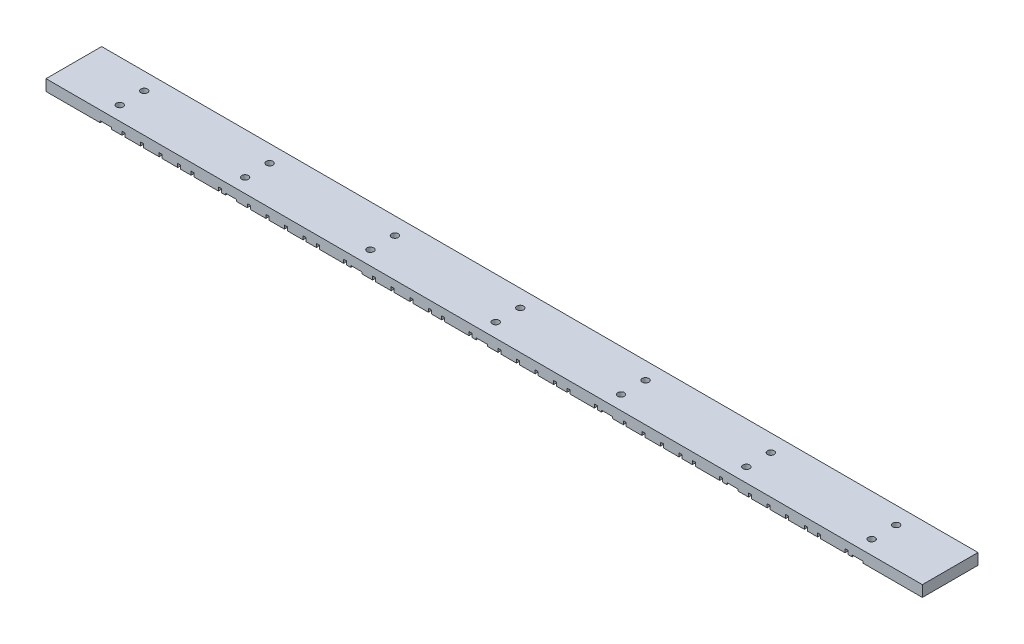
SolidWorks part; units mm, degrees
ref_plane "Front Plane" through (0, 0, 0) normal (0, 0, 1) x (1, 0, 0)
ref_plane "Top Plane" through (0, 0, 0) normal (0, 1, 0) x (1, 0, 0)
ref_plane "Right Plane" through (0, 0, 0) normal (1, 0, 0) x (0, 0, -1)
ref_plane "Plane1" through (0, 98, 0) normal (0, 1, 0) x (1, 0, 0)
sketch "Sketch2" plane through (0, 98, 0) normal (0, 1, 0) x (1, 0, 0)
  line L1 (-100, 51.75) -> (400, 51.75)
  line L2 (-100, 51.75) -> (-100, 20)
  line L3 (-100, 20) -> (400, 20)
  line L4 (400, 51.75) -> (400, 20)
extrude "Boss-Extrude1" add sketch "Sketch2" along normal blind 6.35
sketch "Sketch5" plane through (0, 0, -51.75) normal (0, 0, -1) x (-1, 0, 0)
  line L0 (-357.5571, 98) -> (-357.5571, 100.0571)
  line L1 (-357.5571, 100.0571) -> (-355.8553, 100.0571)
  line L2 (-355.8553, 100.0571) -> (-355.8553, 98)
  line L3 (-355.8553, 98) -> (-341.9571, 98)
  line L4 (-341.9571, 98) -> (-341.9571, 100.0571)
  line L5 (-341.9571, 100.0571) -> (-340.2553, 100.0571)
  line L6 (-340.2553, 100.0571) -> (-340.2553, 98)
  line L7 (-340.2553, 98) -> (-334.3571, 98)
  line L8 (-334.3571, 98) -> (-334.3571, 100.0571)
  line L9 (-334.3571, 100.0571) -> (-332.6553, 100.0571)
  line L10 (-332.6553, 100.0571) -> (-332.6553, 98)
  line L11 (-332.6553, 98) -> (-323.7571, 98)
  line L12 (-323.7571, 98) -> (-323.7571, 100.0571)
  line L13 (-323.7571, 100.0571) -> (-322.0554, 100.0571)
  line L14 (-322.0554, 100.0571) -> (-322.0554, 98)
  line L15 (-322.0554, 98) -> (-313.1572, 98)
  line L16 (-313.1572, 98) -> (-313.1572, 100.0571)
  line L17 (-313.1572, 100.0571) -> (-311.4554, 100.0571)
  line L18 (-311.4554, 100.0571) -> (-311.4554, 98)
  line L19 (-311.4554, 98) -> (-302.5571, 98)
  line L20 (-302.5571, 98) -> (-302.5571, 100.0571)
  line L21 (-302.5571, 100.0571) -> (-300.8554, 100.0571)
  line L22 (-300.8554, 100.0571) -> (-300.8554, 98)
  line L23 (-300.8554, 98) -> (-295.7895, 98)
  line L24 (-400, 98) -> (100, 98) construction
  line L25 (-295.7895, 98) -> (-295.7895, 96.6332)
  line L27 (-295.7895, 96.6332) -> (-359.0747, 96.6332)
  line L28 (-359.0747, 96.6332) -> (-359.0747, 98)
  line L29 (-359.0747, 98) -> (-357.5571, 98)
  line L30 (-286.0571, 98) -> (-286.0571, 100.0571)
  line L31 (-286.0571, 100.0571) -> (-284.3553, 100.0571)
  line L32 (-284.3553, 100.0571) -> (-284.3553, 98)
  line L33 (-284.3553, 98) -> (-270.4571, 98)
  line L34 (-270.4571, 98) -> (-270.4571, 100.0571)
  line L35 (-270.4571, 100.0571) -> (-268.7553, 100.0571)
  line L36 (-268.7553, 100.0571) -> (-268.7553, 98)
  line L37 (-268.7553, 98) -> (-262.8571, 98)
  line L38 (-262.8571, 98) -> (-262.8571, 100.0571)
  line L39 (-262.8571, 100.0571) -> (-261.1553, 100.0571)
  line L40 (-261.1553, 100.0571) -> (-261.1553, 98)
  line L41 (-261.1553, 98) -> (-252.2571, 98)
  line L42 (-252.2571, 98) -> (-252.2571, 100.0571)
  line L43 (-252.2571, 100.0571) -> (-250.5554, 100.0571)
  line L44 (-250.5554, 100.0571) -> (-250.5554, 98)
  line L45 (-250.5554, 98) -> (-241.6572, 98)
  line L46 (-241.6572, 98) -> (-241.6572, 100.0571)
  line L47 (-241.6572, 100.0571) -> (-239.9554, 100.0571)
  line L48 (-239.9554, 100.0571) -> (-239.9554, 98)
  line L49 (-239.9554, 98) -> (-231.0571, 98)
  line L50 (-231.0571, 98) -> (-231.0571, 100.0571)
  line L51 (-231.0571, 100.0571) -> (-229.3554, 100.0571)
  line L52 (-229.3554, 100.0571) -> (-229.3554, 98)
  line L53 (-229.3554, 98) -> (-224.2895, 98)
  line L54 (-224.2895, 98) -> (-224.2895, 96.6332)
  line L55 (-224.2895, 96.6332) -> (-287.5747, 96.6332)
  line L56 (-287.5747, 96.6332) -> (-287.5747, 98)
  line L57 (-287.5747, 98) -> (-286.0571, 98)
  line L58 (-214.5572, 98) -> (-214.5572, 100.0571)
  line L59 (-214.5572, 100.0571) -> (-212.8554, 100.0571)
  line L60 (-212.8554, 100.0571) -> (-212.8554, 98)
  line L61 (-212.8554, 98) -> (-198.9571, 98)
  line L62 (-198.9571, 98) -> (-198.9571, 100.0571)
  line L63 (-198.9571, 100.0571) -> (-197.2553, 100.0571)
  line L64 (-197.2553, 100.0571) -> (-197.2553, 98)
  line L65 (-197.2553, 98) -> (-191.3571, 98)
  line L66 (-191.3571, 98) -> (-191.3571, 100.0571)
  line L67 (-191.3571, 100.0571) -> (-189.6554, 100.0571)
  line L68 (-189.6554, 100.0571) -> (-189.6554, 98)
  line L69 (-189.6554, 98) -> (-180.7571, 98)
  line L70 (-180.7571, 98) -> (-180.7571, 100.0571)
  line L71 (-180.7571, 100.0571) -> (-179.0554, 100.0571)
  line L72 (-179.0554, 100.0571) -> (-179.0554, 98)
  line L73 (-179.0554, 98) -> (-170.1572, 98)
  line L74 (-170.1572, 98) -> (-170.1572, 100.0571)
  line L75 (-170.1572, 100.0571) -> (-168.4554, 100.0571)
  line L76 (-168.4554, 100.0571) -> (-168.4554, 98)
  line L77 (-168.4554, 98) -> (-159.5572, 98)
  line L78 (-159.5572, 98) -> (-159.5572, 100.0571)
  line L79 (-159.5572, 100.0571) -> (-157.8554, 100.0571)
  line L80 (-157.8554, 100.0571) -> (-157.8554, 98)
  line L81 (-157.8554, 98) -> (-152.7895, 98)
  line L82 (-152.7895, 98) -> (-152.7895, 96.6332)
  line L83 (-152.7895, 96.6332) -> (-216.0747, 96.6332)
  line L84 (-216.0747, 96.6332) -> (-216.0747, 98)
  line L85 (-216.0747, 98) -> (-214.5572, 98)
  line L86 (-143.0572, 98) -> (-143.0572, 100.0571)
  line L87 (-143.0572, 100.0571) -> (-141.3554, 100.0571)
  line L88 (-141.3554, 100.0571) -> (-141.3554, 98)
  line L89 (-141.3554, 98) -> (-127.4571, 98)
  line L90 (-127.4571, 98) -> (-127.4571, 100.0571)
  line L91 (-127.4571, 100.0571) -> (-125.7553, 100.0571)
  line L92 (-125.7553, 100.0571) -> (-125.7553, 98)
  line L93 (-125.7553, 98) -> (-119.8572, 98)
  line L94 (-119.8572, 98) -> (-119.8572, 100.0571)
  line L95 (-119.8572, 100.0571) -> (-118.1554, 100.0571)
  line L96 (-118.1554, 100.0571) -> (-118.1554, 98)
  line L97 (-118.1554, 98) -> (-109.2572, 98)
  line L98 (-109.2572, 98) -> (-109.2572, 100.0571)
  line L99 (-109.2572, 100.0571) -> (-107.5554, 100.0571)
  line L100 (-107.5554, 100.0571) -> (-107.5554, 98)
  line L101 (-107.5554, 98) -> (-98.6572, 98)
  line L102 (-98.6572, 98) -> (-98.6572, 100.0571)
  line L103 (-98.6572, 100.0571) -> (-96.9554, 100.0571)
  line L104 (-96.9554, 100.0571) -> (-96.9554, 98)
  line L105 (-96.9554, 98) -> (-88.0572, 98)
  line L106 (-88.0572, 98) -> (-88.0572, 100.0571)
  line L107 (-88.0572, 100.0571) -> (-86.3554, 100.0571)
  line L108 (-86.3554, 100.0571) -> (-86.3554, 98)
  line L109 (-86.3554, 98) -> (-81.2895, 98)
  line L110 (-81.2895, 98) -> (-81.2895, 96.6332)
  line L111 (-81.2895, 96.6332) -> (-144.5747, 96.6332)
  line L112 (-144.5747, 96.6332) -> (-144.5747, 98)
  line L113 (-144.5747, 98) -> (-143.0572, 98)
  line L114 (-71.5572, 98) -> (-71.5572, 100.0571)
  line L115 (-71.5572, 100.0571) -> (-69.8554, 100.0571)
  line L116 (-69.8554, 100.0571) -> (-69.8554, 98)
  line L117 (-69.8554, 98) -> (-55.9571, 98)
  line L118 (-55.9571, 98) -> (-55.9571, 100.0571)
  line L119 (-55.9571, 100.0571) -> (-54.2553, 100.0571)
  line L120 (-54.2553, 100.0571) -> (-54.2553, 98)
  line L121 (-54.2553, 98) -> (-48.3572, 98)
  line L122 (-48.3572, 98) -> (-48.3572, 100.0571)
  line L123 (-48.3572, 100.0571) -> (-46.6554, 100.0571)
  line L124 (-46.6554, 100.0571) -> (-46.6554, 98)
  line L125 (-46.6554, 98) -> (-37.7572, 98)
  line L126 (-37.7572, 98) -> (-37.7572, 100.0571)
  line L127 (-37.7572, 100.0571) -> (-36.0554, 100.0571)
  line L128 (-36.0554, 100.0571) -> (-36.0554, 98)
  line L129 (-36.0554, 98) -> (-27.1572, 98)
  line L130 (-27.1572, 98) -> (-27.1572, 100.0571)
  line L131 (-27.1572, 100.0571) -> (-25.4554, 100.0571)
  line L132 (-25.4554, 100.0571) -> (-25.4554, 98)
  line L133 (-25.4554, 98) -> (-16.5572, 98)
  line L134 (-16.5572, 98) -> (-16.5572, 100.0571)
  line L135 (-16.5572, 100.0571) -> (-14.8554, 100.0571)
  line L136 (-14.8554, 100.0571) -> (-14.8554, 98)
  line L137 (-14.8554, 98) -> (-9.7895, 98)
  line L138 (-9.7895, 98) -> (-9.7895, 96.6332)
  line L139 (-9.7895, 96.6332) -> (-73.0747, 96.6332)
  line L140 (-73.0747, 96.6332) -> (-73.0747, 98)
  line L141 (-73.0747, 98) -> (-71.5572, 98)
  line L142 (-0.0572, 98) -> (-0.0572, 100.0571)
  line L143 (-0.0572, 100.0571) -> (1.6446, 100.0571)
  line L144 (1.6446, 100.0571) -> (1.6446, 98)
  line L145 (1.6446, 98) -> (15.5429, 98)
  line L146 (15.5429, 98) -> (15.5429, 100.0571)
  line L147 (15.5429, 100.0571) -> (17.2447, 100.0571)
  line L148 (17.2447, 100.0571) -> (17.2447, 98)
  line L149 (17.2447, 98) -> (23.1428, 98)
  line L150 (23.1428, 98) -> (23.1428, 100.0571)
  line L151 (23.1428, 100.0571) -> (24.8446, 100.0571)
  line L152 (24.8446, 100.0571) -> (24.8446, 98)
  line L153 (24.8446, 98) -> (33.7428, 98)
  line L154 (33.7428, 98) -> (33.7428, 100.0571)
  line L155 (33.7428, 100.0571) -> (35.4446, 100.0571)
  line L156 (35.4446, 100.0571) -> (35.4446, 98)
  line L157 (35.4446, 98) -> (44.3428, 98)
  line L158 (44.3428, 98) -> (44.3428, 100.0571)
  line L159 (44.3428, 100.0571) -> (46.0446, 100.0571)
  line L160 (46.0446, 100.0571) -> (46.0446, 98)
  line L161 (46.0446, 98) -> (54.9428, 98)
  line L162 (54.9428, 98) -> (54.9428, 100.0571)
  line L163 (54.9428, 100.0571) -> (56.6446, 100.0571)
  line L164 (56.6446, 100.0571) -> (56.6446, 98)
  line L165 (56.6446, 98) -> (61.7105, 98)
  line L166 (61.7105, 98) -> (61.7105, 96.6332)
  line L167 (61.7105, 96.6332) -> (-1.5747, 96.6332)
  line L168 (-1.5747, 96.6332) -> (-1.5747, 98)
  line L169 (-1.5747, 98) -> (-0.0572, 98)
  dimension "D1" = 6
extrude "Cut-Extrude2" cut sketch "Sketch5" against normal through all
sketch "Sketch7" plane through (0, 0, -20) normal (0, 0, 1) x (1, 0, 0)
  line L0 (-70.2467, 98) -> (-69.0919, 98)
  line L1 (-100, 98) -> (-56.6446, 98) construction
  line L2 (-69.0919, 98) -> (-69.0919, 99)
  line L3 (-69.0919, 99) -> (-62.7419, 99)
  line L4 (-62.7419, 99) -> (-62.7419, 98)
  line L5 (-62.7419, 98) -> (-61.7747, 98)
  line L6 (-61.7747, 98) -> (-61.7747, 96.8336)
  line L7 (-61.7747, 96.8336) -> (-70.2467, 96.8336)
  line L8 (-70.2467, 96.8336) -> (-70.2467, 98)
  line L9 (1.2533, 98) -> (2.4081, 98)
  line L10 (2.4081, 98) -> (2.4081, 99)
  line L11 (2.4081, 99) -> (8.7581, 99)
  line L12 (8.7581, 99) -> (8.7581, 98)
  line L13 (8.7581, 98) -> (9.7253, 98)
  line L14 (9.7253, 98) -> (9.7253, 96.8336)
  line L15 (9.7253, 96.8336) -> (1.2533, 96.8336)
  line L16 (1.2533, 96.8336) -> (1.2533, 98)
  line L17 (72.7533, 98) -> (73.9081, 98)
  line L18 (73.9081, 98) -> (73.9081, 99)
  line L19 (73.9081, 99) -> (80.2581, 99)
  line L20 (80.2581, 99) -> (80.2581, 98)
  line L21 (80.2581, 98) -> (81.2253, 98)
  line L22 (81.2253, 98) -> (81.2253, 96.8336)
  line L23 (81.2253, 96.8336) -> (72.7533, 96.8336)
  line L24 (72.7533, 96.8336) -> (72.7533, 98)
  line L25 (144.2533, 98) -> (145.4081, 98)
  line L26 (145.4081, 98) -> (145.4081, 99)
  line L27 (145.4081, 99) -> (151.7581, 99)
  line L28 (151.7581, 99) -> (151.7581, 98)
  line L29 (151.7581, 98) -> (152.7253, 98)
  line L30 (152.7253, 98) -> (152.7253, 96.8336)
  line L31 (152.7253, 96.8336) -> (144.2533, 96.8336)
  line L32 (144.2533, 96.8336) -> (144.2533, 98)
  line L33 (215.7533, 98) -> (216.9081, 98)
  line L34 (216.9081, 98) -> (216.9081, 99)
  line L35 (216.9081, 99) -> (223.2581, 99)
  line L36 (223.2581, 99) -> (223.2581, 98)
  line L37 (223.2581, 98) -> (224.2253, 98)
  line L38 (224.2253, 98) -> (224.2253, 96.8336)
  line L39 (224.2253, 96.8336) -> (215.7533, 96.8336)
  line L40 (215.7533, 96.8336) -> (215.7533, 98)
  line L41 (287.2533, 98) -> (288.4081, 98)
  line L42 (288.4081, 98) -> (288.4081, 99)
  line L43 (288.4081, 99) -> (294.7581, 99)
  line L44 (294.7581, 99) -> (294.7581, 98)
  line L45 (294.7581, 98) -> (295.7253, 98)
  line L46 (295.7253, 98) -> (295.7253, 96.8336)
  line L47 (295.7253, 96.8336) -> (287.2533, 96.8336)
  line L48 (287.2533, 96.8336) -> (287.2533, 98)
  line L49 (358.7533, 98) -> (359.9081, 98)
  line L50 (359.9081, 98) -> (359.9081, 99)
  line L51 (359.9081, 99) -> (366.2581, 99)
  line L52 (366.2581, 99) -> (366.2581, 98)
  line L53 (366.2581, 98) -> (367.2253, 98)
  line L54 (367.2253, 98) -> (367.2253, 96.8336)
  line L55 (367.2253, 96.8336) -> (358.7533, 96.8336)
  line L56 (358.7533, 96.8336) -> (358.7533, 98)
  dimension "D1" = 7
extrude "Cut-Extrude4" cut sketch "Sketch7" against normal through all
sketch "Sketch6" plane through (0, 99, 0) normal (0, 1, 0) x (1, 0, 0)
  line L0 (-65.9169, 20) -> (-65.9169, 51.75) construction
  line L1 (-62.7419, 20) -> (-69.0919, 20) construction
  line L2 (-62.7419, 51.75) -> (-69.0919, 51.75) construction
  line L3 (-69.0919, 24.331) -> (-65.9169, 24.331) construction
  line L4 (-69.0919, 51.75) -> (-69.0919, 20) construction
  line L5 (-62.7419, 46.2989) -> (-65.9169, 46.2989) construction
  line L6 (-62.7419, 51.75) -> (-62.7419, 20) construction
  circle A0 centre (-65.9169, 28) radius 1.8987
  circle A1 centre (-65.9169, 42) radius 1.8987
  circle A4 centre (5.5831, 28) radius 1.8987
  circle A5 centre (5.5831, 42) radius 1.8987
  circle A6 centre (77.0831, 28) radius 1.8987
  circle A7 centre (77.0831, 42) radius 1.8987
  circle A8 centre (148.5831, 28) radius 1.8987
  circle A9 centre (148.5831, 42) radius 1.8987
  circle A10 centre (220.0831, 28) radius 1.8987
  circle A11 centre (220.0831, 42) radius 1.8987
  circle A12 centre (291.5831, 28) radius 1.8987
  circle A13 centre (291.5831, 42) radius 1.8987
  circle A14 centre (363.0831, 28) radius 1.8987
  circle A15 centre (363.0831, 42) radius 1.8987
  dimension "D1" = 7
extrude "Cut-Extrude3" cut sketch "Sketch6" along normal through all
